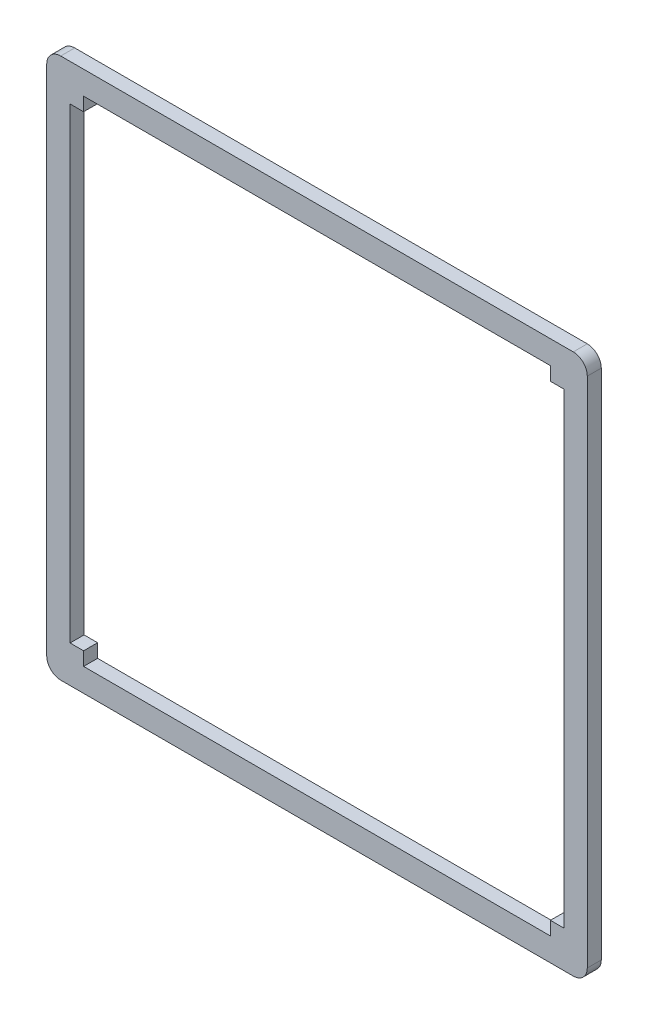
SolidWorks part; units mm, degrees
ref_plane "前视基准面" through (0, 0, 0) normal (0, 0, 1) x (1, 0, 0)
ref_plane "上视基准面" through (0, 0, 0) normal (0, 1, 0) x (1, 0, 0)
ref_plane "右视基准面" through (0, 0, 0) normal (1, 0, 0) x (0, 0, -1)
sketch "草图1" plane through (0, 0, 0) normal (0, 0, 1) x (1, 0, 0)
  line L0 (100, -2.9) -> (0, -2.9)
  line L6 (67.9, 102.9) -> (92.9, 102.9)
  line L13 (7.1, 102.9) -> (32.1, 102.9)
  line L14 (-2.9, 92.9) -> (-2.9, 67.9)
  line L15 (7.1, -2.9) -> (32.1, -2.9)
  line L16 (102.9, 92.9) -> (102.9, 67.9)
  line L19 (-4.9, 107.9) -> (104.9, 107.9)
  line L20 (-7.9, 104.9) -> (-7.9, -4.9)
  line L21 (-4.9, -7.9) -> (104.9, -7.9)
  line L22 (107.9, 104.9) -> (107.9, -4.9)
  line L25 (35, 102.9) -> (65, 102.9)
  line L27 (102.9, 92.9) -> (102.9, 67.9)
  line L30 (102.9, 32.1) -> (102.9, 7.1)
  line L31 (92.9, 102.9) -> (67.9, 102.9)
  line L35 (102.9, 65) -> (102.9, 35)
  line L37 (102.9, 7.1) -> (102.9, 32.1)
  line L40 (35, -2.9) -> (65, -2.9)
  line L41 (92.9, -2.9) -> (67.9, -2.9)
  line L45 (67.9, -2.9) -> (92.9, -2.9)
  line L46 (7.1, -2.9) -> (32.1, -2.9)
  line L50 (-2.9, 32.1) -> (-2.9, 7.1)
  line L52 (-2.9, 7.1) -> (-2.9, 32.1)
  line L55 (-2.9, 65) -> (-2.9, 35)
  line L57 (-2.9, 92.9) -> (-2.9, 67.9)
  line L60 (102.9, 35) -> (102.9, 65)
  line L61 (7.1, 102.9) -> (32.1, 102.9)
  line L65 (35, -2.9) -> (65, -2.9)
  line L67 (102.9, 35) -> (102.9, 65)
  line L70 (-2.9, 65) -> (-2.9, 35)
  line L71 (35, -2.9) -> (65, -2.9)
  line L75 (35, 102.9) -> (65, 102.9)
  line L77 (-2.9, 65) -> (-2.9, 35)
  line L80 (-2.9, 0) -> (-2.9, 100)
  line L81 (35, 102.9) -> (65, 102.9)
  line L85 (0, 102.9) -> (100, 102.9)
  line L94 (102.9, 100) -> (102.9, 0)
  line L115 (102.9, 100) -> (100, 100)
  line L120 (100, 102.9) -> (100, 100)
  line L145 (102.9, 0) -> (100, 0)
  line L146 (100, -2.9) -> (100, 0)
  line L171 (100, -2.9) -> (0, -2.9) construction
  line L172 (102.9, 0) -> (102.9, 100) construction
  line L173 (100, 102.9) -> (0, 102.9) construction
  line L174 (-2.9, 0) -> (-2.9, 100) construction
  line L175 (-2.9, 0) -> (0, 0)
  line L176 (0, -2.9) -> (0, 0)
  line L179 (-2.9, 100) -> (0, 100)
  line L180 (0, 102.9) -> (0, 100)
  arc A2 (104.9, -7.9) -> (107.9, -4.9) centre (104.9, -4.9) ccw
  arc A3 (-4.9, -7.9) -> (-7.9, -4.9) centre (-4.9, -4.9) cw
  arc A4 (-7.9, 104.9) -> (-4.9, 107.9) centre (-4.9, 104.9) cw
  arc A5 (107.9, 104.9) -> (104.9, 107.9) centre (104.9, 104.9) ccw
  point P59 (102.9, 50)
  point P65 (50, -2.9)
  point P71 (-2.9, 50)
  point P77 (50, 102.9)
extrude "凸台-拉伸1" add sketch "草图1" along normal blind 3 contours L22 A5 L19 A4 L20 A3 L21 A2 L85 L94 L16 L35 L30 L0 L80 L50 L55 L14 L13 L25 L6
